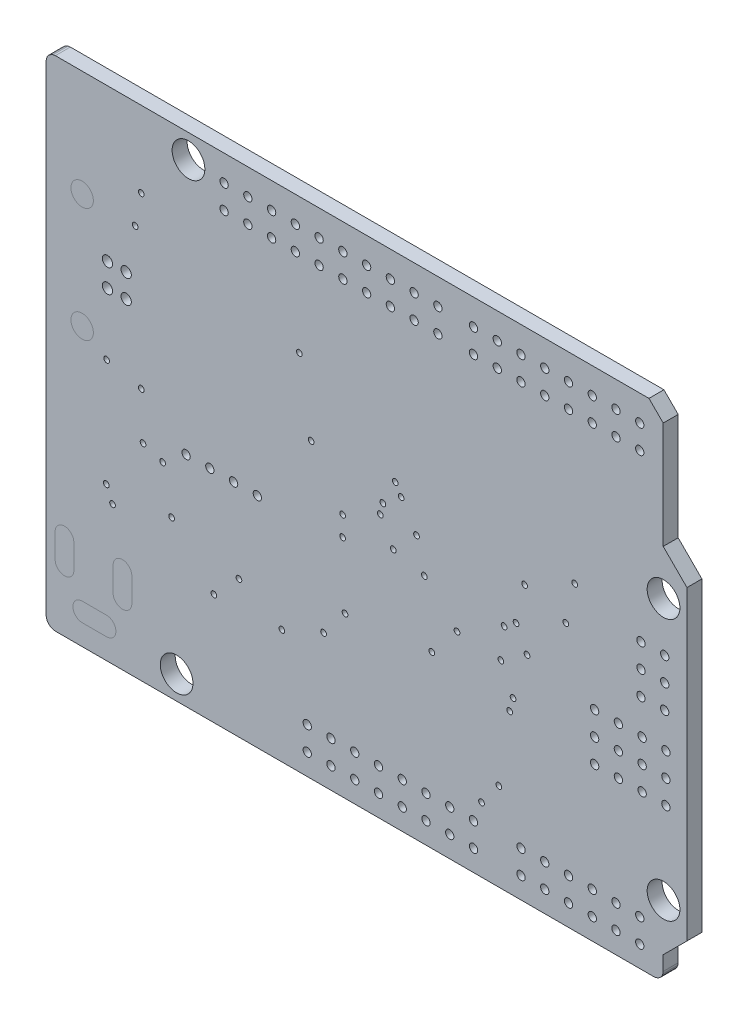
SolidWorks part; units mm, degrees
ref_plane "Front Plane" through (0, 0, 0) normal (0, 0, 1) x (1, 0, 0)
ref_plane "Top Plane" through (0, 0, 0) normal (0, 1, 0) x (1, 0, 0)
ref_plane "Right Plane" through (0, 0, 0) normal (1, 0, 0) x (0, 0, -1)
sketch "Szkic1" plane through (0, 0, 0) normal (0, 0, 1) x (1, 0, 0)
  line L0 (-32.9978, 52.2844) -> (-32.9978, 0.9945)
  line L1 (-32.9978, 0.9945) -> (-32.9554, 0.7406)
  line L2 (-32.9554, 0.7406) -> (-32.8708, 0.5078)
  line L3 (-32.8708, 0.5078) -> (-32.7015, 0.2962)
  line L4 (-32.7015, 0.2962) -> (-32.4899, 0.127)
  line L5 (-32.4899, 0.127) -> (-32.2572, 0.0423)
  line L6 (-32.2572, 0.0423) -> (-32.0033, 0)
  line L7 (-32.0033, 0) -> (32.0033, 0)
  line L8 (32.0033, 0) -> (32.2572, 0.0423)
  line L9 (32.2572, 0.0423) -> (32.4899, 0.127)
  line L10 (32.4899, 0.127) -> (32.7015, 0.2962)
  line L11 (32.7015, 0.2962) -> (32.8708, 0.5078)
  line L12 (32.8708, 0.5078) -> (32.9554, 0.7406)
  line L13 (32.9554, 0.7406) -> (32.9978, 0.9945)
  line L14 (32.9978, 0.9945) -> (32.9978, 2.5391)
  line L15 (32.9978, 2.5391) -> (35.5369, 5.0782)
  line L16 (35.5369, 5.0782) -> (35.5369, 37.8115)
  line L17 (35.5369, 37.8115) -> (32.9978, 40.3506)
  line L18 (32.9978, 40.3506) -> (32.9978, 51.7766)
  line L19 (32.9978, 51.7766) -> (31.4743, 53.3)
  line L20 (31.4743, 53.3) -> (-32.0033, 53.3)
  line L21 (-32.0033, 53.3) -> (-32.2572, 53.2577)
  line L22 (-32.2572, 53.2577) -> (-32.4899, 53.1519)
  line L23 (-32.4899, 53.1519) -> (-32.7015, 53.0038)
  line L24 (-32.7015, 53.0038) -> (-32.8708, 52.7922)
  line L25 (-32.8708, 52.7922) -> (-32.9554, 52.5594)
  line L26 (-32.9554, 52.5594) -> (-32.9978, 52.2844)
  circle A0 centre (-19.0398, 2.52) radius 1.75
  circle A1 centre (33.0302, 7.6) radius 1.75
  circle A2 centre (33.0302, 35.54) radius 1.75
  circle A3 centre (-17.7698, 50.78) radius 1.75
  point P35 (0, 0)
extrude "Dodanie-wyciągnięcie1" add sketch "Szkic1" along normal blind 1.6
sketch "Szkic2" plane through (0, 0, 1.6) normal (0, 0, 1) x (1, 0, 0)
  line L0 (-30.0296, 9.2181) -> (-30.0296, 6.6181)
  line L1 (-32.0296, 6.6181) -> (-32.0296, 9.2181)
  line L2 (-26.5297, 4.2179) -> (-29.1297, 4.2179)
  line L3 (-29.1297, 2.2179) -> (-26.5297, 2.2179)
  line L4 (-23.83, 6.6181) -> (-23.83, 9.2181)
  line L5 (-25.83, 6.6181) -> (-25.83, 9.2181)
  circle A0 centre (-10.4038, 23.348) radius 0.4445
  circle A1 centre (-12.9438, 23.348) radius 0.4445
  circle A2 centre (-15.4838, 23.348) radius 0.4445
  circle A3 centre (-18.0238, 23.348) radius 0.4445
  circle A4 centre (-26.4317, 34.544) radius 0.55
  circle A5 centre (-26.4317, 37.044) radius 0.55
  circle A6 centre (-24.4317, 34.544) radius 0.55
  circle A7 centre (-24.4317, 37.044) radius 0.55
  circle A8 centre (-5.0698, 4.806) radius 0.4445
  circle A9 centre (-5.0698, 2.266) radius 0.4445
  circle A10 centre (-2.5298, 2.266) radius 0.4445
  circle A11 centre (-2.5298, 4.806) radius 0.4445
  circle A12 centre (0.0102, 2.266) radius 0.4445
  circle A13 centre (0.0102, 4.806) radius 0.4445
  circle A14 centre (2.5502, 4.806) radius 0.4445
  circle A15 centre (2.5502, 2.266) radius 0.4445
  circle A16 centre (5.0902, 2.266) radius 0.4445
  circle A17 centre (5.0902, 4.806) radius 0.4445
  circle A18 centre (7.6302, 2.266) radius 0.4445
  circle A19 centre (7.6302, 4.806) radius 0.4445
  circle A20 centre (10.1702, 4.806) radius 0.4445
  circle A21 centre (10.1702, 2.266) radius 0.4445
  circle A22 centre (12.7102, 2.266) radius 0.4445
  circle A23 centre (12.7102, 4.806) radius 0.4445
  circle A24 centre (17.7902, 2.266) radius 0.4445
  circle A25 centre (17.7902, 4.806) radius 0.4445
  circle A26 centre (20.3302, 4.806) radius 0.4445
  circle A27 centre (20.3302, 2.266) radius 0.4445
  circle A28 centre (22.8702, 2.266) radius 0.4445
  circle A29 centre (22.8702, 4.806) radius 0.4445
  circle A30 centre (25.4102, 4.806) radius 0.4445
  circle A31 centre (25.4102, 2.266) radius 0.4445
  circle A32 centre (27.9502, 2.266) radius 0.4445
  circle A33 centre (27.9502, 4.806) radius 0.4445
  circle A34 centre (30.4902, 4.806) radius 0.4445
  circle A35 centre (30.4902, 2.266) radius 0.4445
  circle A36 centre (33.2842, 16.49) radius 0.4445
  circle A37 centre (30.7442, 16.49) radius 0.4445
  circle A38 centre (28.2042, 16.49) radius 0.4445
  circle A39 centre (25.6642, 16.49) radius 0.4445
  circle A40 centre (25.6642, 19.03) radius 0.4445
  circle A41 centre (28.2042, 19.03) radius 0.4445
  circle A42 centre (30.7442, 19.03) radius 0.4445
  circle A43 centre (33.2842, 19.03) radius 0.4445
  circle A44 centre (33.2842, 21.57) radius 0.4445
  circle A45 centre (30.7442, 21.57) radius 0.4445
  circle A46 centre (28.2042, 21.57) radius 0.4445
  circle A47 centre (25.6642, 21.57) radius 0.4445
  circle A48 centre (30.6172, 25.253) radius 0.4445
  circle A49 centre (33.1572, 25.253) radius 0.4445
  circle A50 centre (33.1572, 27.793) radius 0.4445
  circle A51 centre (30.6172, 27.793) radius 0.4445
  circle A52 centre (30.6172, 30.333) radius 0.4445
  circle A53 centre (33.1572, 30.333) radius 0.4445
  circle A54 centre (-13.9598, 47.986) radius 0.4445
  circle A55 centre (-11.4198, 47.986) radius 0.4445
  circle A56 centre (-8.8798, 47.986) radius 0.4445
  circle A57 centre (-6.3398, 47.986) radius 0.4445
  circle A58 centre (-3.7998, 47.986) radius 0.4445
  circle A59 centre (-1.2598, 47.986) radius 0.4445
  circle A60 centre (1.2802, 47.986) radius 0.4445
  circle A61 centre (1.2802, 50.526) radius 0.4445
  circle A62 centre (-1.2598, 50.526) radius 0.4445
  circle A63 centre (-3.7998, 50.526) radius 0.4445
  circle A64 centre (-6.3398, 50.526) radius 0.4445
  circle A65 centre (-8.8798, 50.526) radius 0.4445
  circle A66 centre (-11.4198, 50.526) radius 0.4445
  circle A67 centre (-13.9598, 50.526) radius 0.4445
  circle A68 centre (3.8202, 47.986) radius 0.4445
  circle A69 centre (3.8202, 50.526) radius 0.4445
  circle A70 centre (6.3602, 47.986) radius 0.4445
  circle A71 centre (6.3602, 50.526) radius 0.4445
  circle A72 centre (8.9002, 47.986) radius 0.4445
  circle A73 centre (8.9002, 50.526) radius 0.4445
  circle A74 centre (20.3302, 50.526) radius 0.4445
  circle A75 centre (17.7902, 50.526) radius 0.4445
  circle A76 centre (15.2502, 50.526) radius 0.4445
  circle A77 centre (12.7102, 50.526) radius 0.4445
  circle A78 centre (12.7102, 47.986) radius 0.4445
  circle A79 centre (15.2502, 47.986) radius 0.4445
  circle A80 centre (17.7902, 47.986) radius 0.4445
  circle A81 centre (20.3302, 47.986) radius 0.4445
  circle A82 centre (22.8702, 47.986) radius 0.4445
  circle A83 centre (22.8702, 50.526) radius 0.4445
  circle A84 centre (25.4102, 47.986) radius 0.4445
  circle A85 centre (25.4102, 50.526) radius 0.4445
  circle A86 centre (27.9502, 47.986) radius 0.4445
  circle A87 centre (27.9502, 50.526) radius 0.4445
  circle A88 centre (30.4902, 47.986) radius 0.4445
  circle A89 centre (30.4902, 50.526) radius 0.4445
  circle A90 centre (-22.8168, 45.1641) radius 0.305
  circle A91 centre (-23.4696, 41.8087) radius 0.305
  circle A92 centre (-26.5201, 27.8845) radius 0.305
  circle A93 centre (-22.8168, 27.0463) radius 0.305
  circle A94 centre (-5.9106, 38.8192) radius 0.305
  circle A95 centre (-4.6507, 31.3033) radius 0.305
  circle A96 centre (4.346, 31.9866) radius 0.305
  circle A97 centre (4.9708, 30.9071) radius 0.305
  circle A98 centre (2.7432, 28.1943) radius 0.305
  circle A99 centre (3.0201, 29.3704) radius 0.305
  circle A100 centre (6.6167, 28.1867) radius 0.305
  circle A101 centre (4.1275, 25.6467) radius 0.305
  circle A102 centre (-1.2878, 26.1547) radius 0.305
  circle A103 centre (-1.2878, 24.0592) radius 0.305
  circle A104 centre (-1.0312, 17.125) radius 0.305
  circle A105 centre (-22.6288, 22.0958) radius 0.305
  circle A106 centre (-20.5308, 21.3846) radius 0.305
  circle A107 centre (-25.8902, 14.8263) radius 0.305
  circle A108 centre (-26.5582, 16.3376) radius 0.305
  circle A109 centre (-19.5732, 16.7516) radius 0.305
  circle A110 centre (-3.3223, 14.1939) radius 0.305
  circle A111 centre (-7.7825, 12.2431) radius 0.305
  circle A112 centre (-12.3723, 14.6561) radius 0.305
  circle A113 centre (-15.052, 11.8875) radius 0.305
  circle A114 centre (7.4524, 24.8568) radius 0.305
  circle A115 centre (10.9449, 21.4481) radius 0.305
  circle A116 centre (8.2576, 18.202) radius 0.305
  circle A117 centre (13.5687, 6.932) radius 0.305
  circle A118 centre (15.4229, 9.3933) radius 0.305
  circle A119 centre (16.5786, 16.8837) radius 0.305
  circle A120 centre (16.9418, 18.2807) radius 0.305
  circle A121 centre (15.6388, 21.1255) radius 0.305
  circle A122 centre (15.9817, 24.4529) radius 0.305
  circle A123 centre (18.4353, 23.0305) radius 0.305
  circle A124 centre (17.2619, 25.3953) radius 0.305
  circle A125 centre (18.1763, 29.3932) radius 0.305
  circle A126 centre (22.5832, 28.0521) radius 0.305
  circle A127 centre (23.5306, 32.172) radius 0.305
  arc A128 (-30.0296, 9.2181) -> (-32.0296, 9.2181) centre (-31.0296, 9.2181) ccw
  arc A129 (-32.0296, 6.6181) -> (-30.0296, 6.6181) centre (-31.0296, 6.6181) ccw
  arc A130 (-29.1297, 4.2179) -> (-29.1297, 2.2179) centre (-29.1297, 3.2179) ccw
  arc A131 (-26.5297, 2.2179) -> (-26.5297, 4.2179) centre (-26.5297, 3.2179) ccw
  arc A132 (-23.83, 9.2181) -> (-25.83, 9.2181) centre (-24.83, 9.2181) ccw
  arc A133 (-25.83, 6.6181) -> (-23.83, 6.6181) centre (-24.83, 6.6181) ccw
extrude "Wytnij-wyciągnięcie1" cut sketch "Szkic2" against normal through all
sketch "Szkic3" plane through (0, 0, 1.6) normal (0, 0, 1) x (1, 0, 0)
  line L0 (-29.1297, 2.2179) -> (-26.5297, 2.2179) construction
  line L1 (-26.5297, 4.2179) -> (-29.1297, 4.2179) construction
  line L2 (-25.83, 9.2181) -> (-25.83, 6.6181) construction
  line L3 (-23.83, 6.6181) -> (-23.83, 9.2181) construction
  line L4 (-32.0296, 9.2181) -> (-32.0296, 6.6181) construction
  line L5 (-30.0296, 6.6181) -> (-30.0296, 9.2181) construction
  line L6 (-29.1297, 2.2179) -> (-26.5297, 2.2179)
  line L7 (-26.5297, 4.2179) -> (-29.1297, 4.2179)
  line L8 (-25.83, 9.2181) -> (-25.83, 6.6181)
  line L9 (-23.83, 6.6181) -> (-23.83, 9.2181)
  line L10 (-32.0296, 9.2181) -> (-32.0296, 6.6181)
  line L11 (-30.0296, 6.6181) -> (-30.0296, 9.2181)
  arc A0 (-29.1297, 4.2179) -> (-29.1297, 2.2179) centre (-29.1297, 3.2179) ccw construction
  arc A1 (-26.5297, 2.2179) -> (-26.5297, 4.2179) centre (-26.5297, 3.2179) ccw construction
  arc A2 (-25.83, 6.6181) -> (-23.83, 6.6181) centre (-24.83, 6.6181) ccw construction
  arc A3 (-23.83, 9.2181) -> (-25.83, 9.2181) centre (-24.83, 9.2181) ccw construction
  arc A4 (-30.0296, 9.2181) -> (-32.0296, 9.2181) centre (-31.0296, 9.2181) ccw construction
  arc A5 (-32.0296, 6.6181) -> (-30.0296, 6.6181) centre (-31.0296, 6.6181) ccw construction
  arc A6 (-29.1297, 4.2179) -> (-29.1297, 2.2179) centre (-29.1297, 3.2179) ccw
  arc A7 (-26.5297, 2.2179) -> (-26.5297, 4.2179) centre (-26.5297, 3.2179) ccw
  arc A8 (-25.83, 6.6181) -> (-23.83, 6.6181) centre (-24.83, 6.6181) ccw
  arc A9 (-23.83, 9.2181) -> (-25.83, 9.2181) centre (-24.83, 9.2181) ccw
  arc A10 (-30.0296, 9.2181) -> (-32.0296, 9.2181) centre (-31.0296, 9.2181) ccw
  arc A11 (-32.0296, 6.6181) -> (-30.0296, 6.6181) centre (-31.0296, 6.6181) ccw
extrude "Dodanie-wyciągnięcie2" add sketch "Szkic3" against normal up to surface (1.6 mm away) separate body up to face at (25.8547, 50.526, 0)
sketch "Szkic4" plane through (0, 0, 1.6) normal (0, 0, 1) x (1, 0, 0)
  line L0 (-0.2645, 53.3) -> (-0.2645, 68.5013) construction
  line L1 (31.4743, 53.3) -> (-32.0033, 53.3) construction
  circle A0 centre (-29.1419, 29.6777) radius 1.2
  circle A1 centre (-29.1419, 41.9103) radius 1.2
  point P6 (-0.2645, 53.3)
extrude "Wytnij-wyciągnięcie2" cut sketch "Szkic4" against normal through all
sketch "Szkic5" plane through (0, 0, 1.6) normal (0, 0, 1) x (1, 0, 0)
  circle A0 centre (-29.1419, 41.9103) radius 1.2 construction
  circle A1 centre (-29.1419, 41.9103) radius 1.2
  circle A2 centre (-29.1419, 29.6777) radius 1.2 construction
  circle A3 centre (-29.1419, 29.6777) radius 1.2
extrude "Dodanie-wyciągnięcie3" add sketch "Szkic5" against normal up to surface (1.6 mm away) separate body up to face at (-27.9419, 29.6777, 0)
